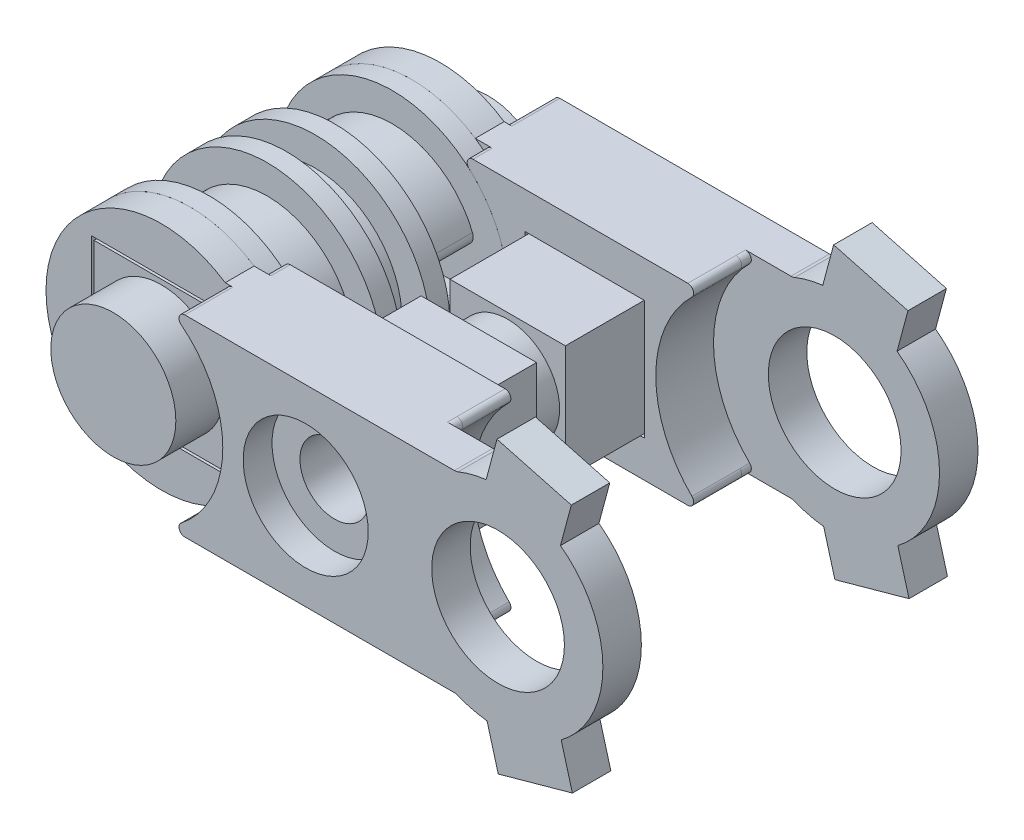
SolidWorks part; units mm, degrees
material "ABS"
ref_plane "正面" through (0, 0, 0) normal (0, 0, 1) x (1, 0, 0)
ref_plane "平面" through (0, 0, 0) normal (0, 1, 0) x (1, 0, 0)
ref_plane "右側面" through (0, 0, 0) normal (1, 0, 0) x (0, 0, -1)
sketch "ｽｹｯﾁ1" plane through (0, 0, 0) normal (0, 0, 1) x (1, 0, 0)
  circle A0 centre (0, 0) radius 4.5
  dimension "D1" = 9
extrude "ﾎﾞｽ - 押し出し1" add sketch "ｽｹｯﾁ1" along normal blind 3
sketch "ｽｹｯﾁ2" plane through (0, 0, 0) normal (0, 0, -1) x (-1, 0, 0)
  circle A0 centre (0, 0) radius 6
  dimension "D1" = 12
extrude "ﾎﾞｽ - 押し出し2" add sketch "ｽｹｯﾁ2" along normal blind 1
sketch "ｽｹｯﾁ3" plane through (0, 0, -1) normal (0, 0, -1) x (-1, 0, 0)
  circle A0 centre (0, 0) radius 4.5 construction
  circle A1 centre (0, 0) radius 4.5
extrude "ﾎﾞｽ - 押し出し3" add sketch "ｽｹｯﾁ3" along normal blind 1.5
sketch "ｽｹｯﾁ4" plane through (0, 0, -2.5) normal (0, 0, -1) x (-1, 0, 0)
  circle A1 centre (0, 0) radius 6
  circle A2 centre (0, 0) radius 6
  dimension "D1" = 0
extrude "ﾎﾞｽ - 押し出し4" add sketch "ｽｹｯﾁ4" along normal blind 1
sketch "ｽｹｯﾁ5" plane through (0, 0, -3.5) normal (0, 0, -1) x (-1, 0, 0)
  circle A0 centre (0, 0) radius 4.5 construction
  circle A1 centre (0, 0) radius 4.5
extrude "ﾎﾞｽ - 押し出し5" add sketch "ｽｹｯﾁ5" along normal blind 3
sketch "ｽｹｯﾁ6" plane through (0, 0, -6.5) normal (0, 0, -1) x (-1, 0, 0)
  circle A1 centre (0, 0) radius 6
  circle A2 centre (0, 0) radius 6
  dimension "D1" = 0
extrude "ﾎﾞｽ - 押し出し6" add sketch "ｽｹｯﾁ6" along normal blind 1
sketch "ｽｹｯﾁ7" plane through (0, 0, 3) normal (0, 0, 1) x (1, 0, 0)
  circle A1 centre (0, 0) radius 6
  circle A2 centre (0, 0) radius 6
  dimension "D1" = 0
extrude "ﾎﾞｽ - 押し出し7" add sketch "ｽｹｯﾁ7" along normal blind 1
sketch "ｽｹｯﾁ10" plane through (0, 0, 4) normal (0, 0, 1) x (1, 0, 0)
  line L1 (3.5, -3.5) -> (-3.5, -3.5)
  line L2 (3.5, -3.5) -> (3.5, 3.5)
  line L3 (3.5, 3.5) -> (-3.5, 3.5)
  line L4 (-3.5, -3.5) -> (-3.5, 3.5)
  line L5 (3.5, -3.5) -> (-3.5, 3.5) construction
  line L6 (3.5, 3.5) -> (-3.5, -3.5) construction
  point P0 (0, 0)
  dimension "D1" = 7
  dimension "D2" = 7
extrude "ﾎﾞｽ - 押し出し10" add sketch "ｽｹｯﾁ10" along normal blind 1.5
sketch "ｽｹｯﾁ11" plane through (0, 0, 5.5) normal (0, 0, 1) x (1, 0, 0)
  circle A0 centre (0, 0) radius 3.25
  dimension "D1" = 6.5
extrude "ﾎﾞｽ - 押し出し11" add sketch "ｽｹｯﾁ11" along normal blind 2.5
ref_plane "平面1" through (0, 0, -1.75) normal (0, 0, 1) x (1, 0, 0)
mirror "ﾐﾗｰ1" about plane through (0, 0, -1.75) normal (0, 0, 1) of "ﾎﾞｽ - 押し出し11", "ﾎﾞｽ - 押し出し10"
sketch "ｽｹｯﾁ12" plane through (0, 0, 4) normal (0, 0, 1) x (1, 0, 0)
  line L0 (0, 0) -> (20, 0) construction
  line L1 (3.3166, 5) -> (16.1672, 5)
  line L3 (16.1672, -5) -> (3.3166, -5)
  line L8 (3.64, -3.64) -> (3.64, 3.64)
  line L9 (-3.64, -3.64) -> (3.64, -3.64)
  line L10 (-3.64, 3.64) -> (-3.64, -3.64)
  line L11 (3.64, 3.64) -> (-3.64, 3.64)
  line L12 (3.64, -3.64) -> (3.64, 3.64)
  line L13 (-3.64, -3.64) -> (3.64, -3.64)
  line L14 (-3.64, 3.64) -> (-3.64, -3.64)
  line L15 (3.64, 3.64) -> (-3.64, 3.64)
  circle A0 centre (0, 0) radius 6 construction
  circle A1 centre (20, 0) radius 3.45 construction
  arc A2 (3.3166, 5) -> (3.3166, -5) centre (0, 0) ccw
  circle A3 centre (20, 0) radius 5.45 construction
  circle A4 centre (20, 0) radius 6.3 construction
  arc A5 (16.1672, 5) -> (16.1672, -5) centre (20, 0) ccw
  circle A6 centre (20, 0) radius 6 construction
  circle A7 centre (0, 0) radius 6 construction
  circle A8 centre (20, 0) radius 3.25 construction
  circle A9 centre (0, 0) radius 3.25 construction
  dimension "D3" = 20
  dimension "D6" = 0.3
  dimension "D2" = 5
  dimension "D7" = 5
  dimension "D4" = 0.2
  dimension "D5" = 2
  dimension "D1" = 0.14
extrude "ﾎﾞｽ - 押し出し12" add sketch "ｽｹｯﾁ12" along normal blind 1.5 separate body
sketch "ｽｹｯﾁ13" plane through (0, 0, 5.5) normal (0, 0, 1) x (1, 0, 0)
  line L6 (16.1672, 5) -> (3.3166, 5) construction
  line L9 (16.1672, 5) -> (3.3166, 5) construction
  line L10 (15.3664, 5) -> (3.7135, 5)
  line L11 (15.3664, -5) -> (3.7135, -5)
  circle A1 centre (0, 0) radius 3.25 construction
  arc A7 (16.1672, 5) -> (16.1672, -5) centre (20, 0) ccw construction
  arc A8 (15.577, 4.4864) -> (15.577, -4.4864) centre (20, 0) ccw
  circle A10 centre (0, 0) radius 5.69 construction
  circle A11 centre (0, 0) radius 3.39 construction
  circle A12 centre (0, 0) radius 5.39 construction
  arc A13 (3.5275, 4.4646) -> (3.5275, -4.4646) centre (0, 0) cw
  arc A14 (15.3664, -5) -> (15.577, -4.4864) centre (15.3664, -4.7) ccw
  arc A15 (15.577, 4.4864) -> (15.3664, 5) centre (15.3664, 4.7) ccw
  arc A16 (3.7135, 5) -> (3.5275, 4.4646) centre (3.7135, 4.7) ccw
  arc A17 (3.5275, -4.4646) -> (3.7135, -5) centre (3.7135, -4.7) ccw
  point P24 (2.7159, 5)
  point P29 (2.7159, -5)
  dimension "D1" = 0.14
  dimension "D3" = 0.3
  dimension "D4" = 2
  dimension "D2" = 0.3
extrude "ﾎﾞｽ - 押し出し13" add sketch "ｽｹｯﾁ13" along normal blind 0.5
fillet "ﾌｨﾚｯﾄ9" radius 0.3 2 edges at (16.1672, -5, 4.75) (16.1672, 5, 4.75)
sketch "ｽｹｯﾁ14" plane through (0, 0, 6) normal (0, 0, 1) x (1, 0, 0)
  line L0 (3.7135, 5) -> (17.7301, 5)
  line L3 (3.7135, -5) -> (17.7301, -5)
  arc A0 (17.7301, 5) -> (17.9208, 5.0378) centre (17.7301, 5.5) ccw
  arc A1 (17.7301, -5) -> (17.9208, -5.0378) centre (17.7301, -5.5) cw
  arc A4 (3.5275, -4.4646) -> (3.7135, -5) centre (3.7135, -4.7) ccw construction
  arc A7 (3.5275, -4.4646) -> (3.5275, 4.4646) centre (0, 0) ccw construction
  arc A8 (3.7135, 5) -> (3.5275, 4.4646) centre (3.7135, 4.7) ccw construction
  arc A9 (3.5275, -4.4646) -> (3.7135, -5) centre (3.7135, -4.7) ccw
  arc A10 (3.7135, 5) -> (3.5275, 4.4646) centre (3.7135, 4.7) ccw
  arc A11 (3.5275, -4.4646) -> (3.5275, 4.4646) centre (0, 0) ccw
  circle A12 centre (20, 0) radius 5.45 construction
  arc A13 (17.9208, 5.0378) -> (17.9208, -5.0378) centre (20, 0) cw
  circle A14 centre (20, 0) radius 3.45 construction
  circle A15 centre (20, 0) radius 3.45
  point P19 (17.8315, -5)
  point P22 (17.8315, 5)
  point P24 (17.8315, 5)
  point P27 (17.8315, -5)
  dimension "D1" = 0.5
extrude "ﾎﾞｽ - 押し出し14" add sketch "ｽｹｯﾁ14" along normal blind 2
sketch "ｽｹｯﾁ15" plane through (0, 0, 4) normal (0, 0, -1) x (-1, 0, 0)
  line L0 (-15.3664, 5) -> (-4.1952, 5)
  line L1 (-3.3166, 5) -> (-16.1672, 5) construction
  line L2 (-15.3664, -5) -> (-4.1952, -5)
  line L3 (-16.1672, -5) -> (-3.3166, -5) construction
  circle A2 centre (0, 0) radius 6 construction
  arc A3 (-3.9955, 4.4762) -> (-3.9955, -4.4762) centre (0, 0) ccw
  arc A7 (-4.1952, -5) -> (-3.9955, -4.4762) centre (-4.1952, -4.7) ccw
  arc A8 (-4.1952, 5) -> (-3.9955, 4.4762) centre (-4.1952, 4.7) cw
  arc A10 (-15.577, -4.4864) -> (-15.3664, -5) centre (-15.3664, -4.7) ccw construction
  arc A11 (-15.577, -4.4864) -> (-15.577, 4.4864) centre (-20, 0) ccw construction
  arc A12 (-15.3664, 5) -> (-15.577, 4.4864) centre (-15.3664, 4.7) ccw construction
  arc A13 (-15.577, -4.4864) -> (-15.3664, -5) centre (-15.3664, -4.7) ccw
  arc A14 (-15.577, -4.4864) -> (-15.577, 4.4864) centre (-20, 0) ccw
  arc A15 (-15.3664, 5) -> (-15.577, 4.4864) centre (-15.3664, 4.7) ccw
  point P26 (-3.3166, -5)
  point P29 (-3.3166, 5)
  dimension "D2" = 0.3
extrude "ﾎﾞｽ - 押し出し15" add sketch "ｽｹｯﾁ15" along normal blind 1
mirror "ﾐﾗｰ2" about plane through (0, 0, -1.75) normal (0, 0, 1) of bodies 116
sketch "ｽｹｯﾁ16" plane through (0, 0, 8) normal (0, 0, 1) x (1, 0, 0)
  line L0 (0, 0) -> (20, 0) construction
  circle A0 centre (20, 0) radius 3.45 construction
  circle A1 centre (10, 0) radius 1.8
  dimension "D1" = 3.6
extrude "ｶｯﾄ - 押し出し1" cut sketch "ｽｹｯﾁ16" against normal through all
sketch "ｽｹｯﾁ17" plane through (0, 0, -6.5) normal (0, 0, 1) x (1, 0, 0)
  line L1 (13.1, -3.1) -> (6.9, -3.1)
  line L2 (13.1, -3.1) -> (13.1, 3.1)
  line L3 (13.1, 3.1) -> (6.9, 3.1)
  line L4 (6.9, -3.1) -> (6.9, 3.1)
  line L5 (13.1, -3.1) -> (6.9, 3.1) construction
  line L6 (13.1, 3.1) -> (6.9, -3.1) construction
  point P0 (10, 0)
  dimension "D2" = 6.2
  dimension "D1" = 6.2
extrude "ｶｯﾄ - 押し出し2" cut sketch "ｽｹｯﾁ17" against normal blind 2
sketch "ｽｹｯﾁ18" plane through (0, 0, 3) normal (0, 0, -1) x (-1, 0, 0)
  line L0 (-7, 3) -> (-13, 3)
  line L5 (-13, 3) -> (-13, -3)
  line L6 (-13, -3) -> (-7, -3)
  line L7 (-7, -3) -> (-7, 3)
  line L8 (-13.1, -3.1) -> (-6.9, -3.1)
  line L9 (-6.9, -3.1) -> (-6.9, 3.1)
  line L10 (-6.9, 3.1) -> (-13.1, 3.1)
  line L11 (-13.1, 3.1) -> (-13.1, -3.1)
  line L12 (-13.1, -3.1) -> (-6.9, -3.1) construction
  line L13 (-6.9, -3.1) -> (-6.9, 3.1) construction
  line L14 (-6.9, 3.1) -> (-13.1, 3.1) construction
  line L15 (-13.1, 3.1) -> (-13.1, -3.1) construction
  dimension "D1" = 0
  dimension "D2" = 0.1
extrude "ﾎﾞｽ - 押し出し16" add sketch "ｽｹｯﾁ18" along normal up to surface (11.5 mm away) up to face at (10, 0, -8.5)
sketch "ｽｹｯﾁ19" plane through (0, 0, 3) normal (0, 0, 1) x (1, 0, 0)
  circle A0 centre (10, 0) radius 1.8 construction
  circle A1 centre (10, 0) radius 1.8
extrude "ｶｯﾄ - 押し出し3" cut sketch "ｽｹｯﾁ19" against normal through all
sketch "ｽｹｯﾁ20" plane through (0, 0, -1.75) normal (0, 0, 1) x (1, 0, 0)
  line L4 (13, 3) -> (7, 3)
  line L5 (13, -3) -> (13, 3)
  line L6 (7, -3) -> (13, -3)
  line L7 (7, 3) -> (7, -3)
  line L8 (13, 3) -> (7, 3)
  line L9 (13, -3) -> (13, 3)
  line L10 (7, -3) -> (13, -3)
  line L11 (7, 3) -> (7, -3)
  circle A1 centre (10, 0) radius 2.7
  dimension "D2" = 5.4
  dimension "D1" = 0
extrude "ｶｯﾄ - 押し出し4" cut sketch "ｽｹｯﾁ20" against normal blind 0.75 and the other way blind 0.75
sketch "ｽｹｯﾁ21" plane through (0, 0, 8) normal (0, 0, 1) x (1, 0, 0)
  circle A0 centre (10, 0) radius 3.25
  dimension "D1" = 6.5
extrude "ｶｯﾄ - 押し出し5" cut sketch "ｽｹｯﾁ21" against normal blind 1.5
sketch "ｽｹｯﾁ22" plane through (0, 0, -11.5) normal (0, 0, -1) x (-1, 0, 0)
  line L1 (-11.6743, 2.9) -> (-13.3486, 0)
  line L2 (-13.3486, 0) -> (-11.6743, -2.9)
  line L3 (-11.6743, -2.9) -> (-8.3257, -2.9)
  line L4 (-8.3257, -2.9) -> (-6.6514, 0)
  line L5 (-6.6514, 0) -> (-8.3257, 2.9)
  line L6 (-8.3257, 2.9) -> (-11.6743, 2.9)
  circle A0 centre (-10, 0) radius 2.9 construction
  dimension "D1" = 5.8
extrude "ｶｯﾄ - 押し出し6" cut sketch "ｽｹｯﾁ22" against normal blind 1
sketch "ｽｹｯﾁ23" plane through (0, 0, 8) normal (0, 0, 1) x (1, 0, 0)
  line L0 (20, 0) -> (21.4106, 5.2643) construction
  line L1 (19.0128, 4.0433) -> (22.8765, 3.008)
  line L2 (19.0128, 4.0433) -> (19.9446, 7.5206)
  line L3 (19.9446, 7.5206) -> (23.8083, 6.4853)
  line L4 (22.8765, 3.008) -> (23.8083, 6.4853)
  line L5 (19.0128, 4.0433) -> (23.8083, 6.4853) construction
  line L6 (19.9446, 7.5206) -> (22.8765, 3.008) construction
  line L7 (20, 0) -> (20, 5.45) construction
  line L8 (20, 0) -> (20, -5.45) construction
  line L9 (20, 0) -> (21.4564, -5.2518) construction
  line L10 (20.0102, -7.5208) -> (23.8647, -6.4518)
  line L11 (20.0102, -7.5208) -> (19.0482, -4.0517)
  line L12 (23.8647, -6.4518) -> (22.9027, -2.9828)
  line L13 (19.0482, -4.0517) -> (22.9027, -2.9828)
  line L14 (20.0102, -7.5208) -> (22.9027, -2.9828) construction
  line L15 (23.8647, -6.4518) -> (19.0482, -4.0517) construction
  arc A0 (17.9208, -5.0378) -> (17.9208, 5.0378) centre (20, 0) ccw construction
  point P0 (21.4106, 5.2643)
  dimension "D1" = 1.8
  dimension "D2" = 4
  dimension "D3" = 15
  dimension "D4" = 15.5
extrude "ﾎﾞｽ - 押し出し17" add sketch "ｽｹｯﾁ23" against normal up to surface (2 mm away) up to face at (17.3986, 0, 6)
sketch "ｽｹｯﾁ24" plane through (0, 0, -11.5) normal (0, 0, -1) x (-1, 0, 0)
  line L12 (-22.8765, 3.008) -> (-19.0128, 4.0433)
  line L13 (-23.8083, 6.4853) -> (-22.8765, 3.008)
  line L14 (-19.9446, 7.5206) -> (-23.8083, 6.4853)
  line L15 (-19.0128, 4.0433) -> (-19.9446, 7.5206)
  line L16 (-22.8765, 3.008) -> (-19.0128, 4.0433)
  line L17 (-23.8083, 6.4853) -> (-22.8765, 3.008)
  line L18 (-19.9446, 7.5206) -> (-23.8083, 6.4853)
  line L19 (-19.0128, 4.0433) -> (-19.9446, 7.5206)
  line L20 (-23.8647, -6.4518) -> (-20.0102, -7.5208)
  line L21 (-22.9027, -2.9828) -> (-23.8647, -6.4518)
  line L22 (-19.0482, -4.0517) -> (-22.9027, -2.9828)
  line L23 (-20.0102, -7.5208) -> (-19.0482, -4.0517)
  line L24 (-23.8647, -6.4518) -> (-20.0102, -7.5208)
  line L25 (-22.9027, -2.9828) -> (-23.8647, -6.4518)
  line L26 (-19.0482, -4.0517) -> (-22.9027, -2.9828)
  line L27 (-20.0102, -7.5208) -> (-19.0482, -4.0517)
  dimension "D1" = 0
  dimension "D2" = 0
extrude "ﾎﾞｽ - 押し出し18" add sketch "ｽｹｯﾁ24" against normal up to surface (2 mm away) up to face at (17.3986, 0, -9.5)
ref_plane "平面2" through (-4.5, 0, 0) normal (-1, 0, 0) x (0, 0, 1)
sketch "ｽｹｯﾁ25" plane through (-4.5, 0, 0) normal (-1, 0, 0) x (0, 0, 1)
  line L0 (-6.5, 0) -> (3, 0) construction
  line L1 (-6.5, -4.5) -> (-6.5, 4.5) construction
  line L2 (3, 4.5) -> (3, -4.5) construction
  line L3 (-3.5, 4.5) -> (-3.5, -4.5) construction
  line L4 (-6.5, -1) -> (-3.5, -1)
  line L5 (-6.5, -1) -> (-6.5, 1)
  line L6 (-6.5, 1) -> (-3.5, 1)
  line L7 (-3.5, -1) -> (-3.5, 1)
  line L8 (0, -4.5) -> (0, 4.5) construction
  line L9 (0, -1) -> (3, -1)
  line L10 (0, -1) -> (0, 1)
  line L11 (0, 1) -> (3, 1)
  line L12 (3, -1) -> (3, 1)
  line L13 (3, 6) -> (3, -6) construction
  dimension "D1" = 2
  dimension "D2" = 1
extrude "ｶｯﾄ - 押し出し7" cut sketch "ｽｹｯﾁ25" against normal through all
fillet "ﾌｨﾚｯﾄ10" radius 0.5 8 edges at (4.3875, -1, 1.5) (-4.3875, -1, 1.5) (-4.3875, 1, 1.5) (4.3875, 1, 1.5) (-4.3875, -1, -5) (4.3875, -1, -5) (4.3875, 1, -5) (-4.3875, 1, -5)
equation "\"D7@ｽｹｯﾁ12\"=\"D2@ｽｹｯﾁ12\""
equation "\"D1@ｽｹｯﾁ17\"=\"D2@ｽｹｯﾁ17\""
equation "\"D2@ｽｹｯﾁ25\"=\"D1@ｽｹｯﾁ25\"/2"
